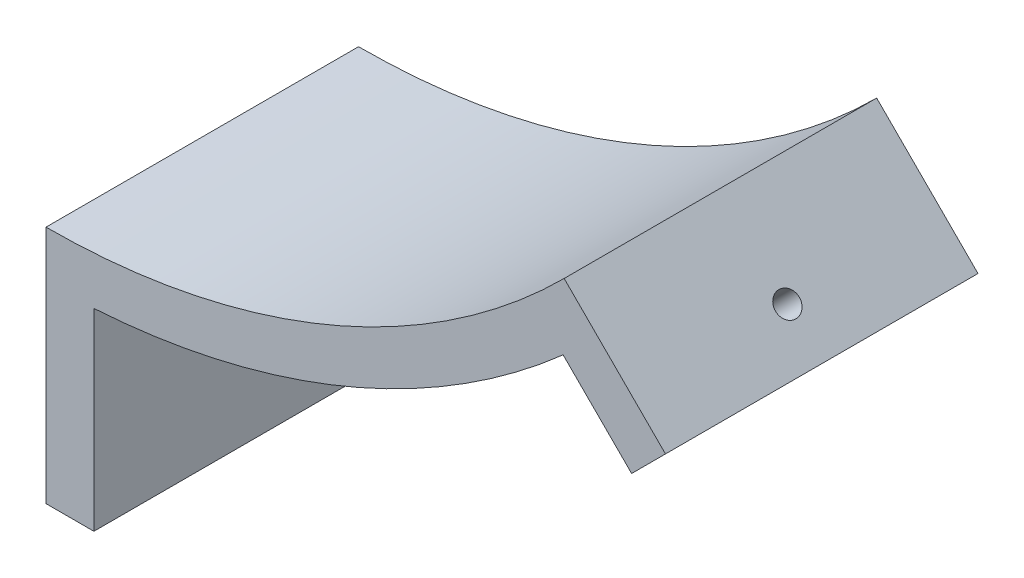
SolidWorks part; units mm, degrees
ref_plane "Alzado" through (0, 0, 0) normal (0, 0, 1) x (1, 0, 0)
ref_plane "Planta" through (0, 0, 0) normal (0, 1, 0) x (1, 0, 0)
ref_plane "Vista lateral" through (0, 0, 0) normal (1, 0, 0) x (0, 0, -1)
sketch "Croquis1" plane through (0, 0, 0) normal (0, 0, 1) x (1, 0, 0)
  line L0 (0, 0) -> (73.1376, 0)
  line L1 (108.1873, -108.1873) -> (129.3428, -129.3428)
  line L4 (0, 0) -> (108.1873, -108.1873)
  line L6 (129.3428, -129.3428) -> (122.2717, -136.4138)
  line L8 (122.2717, -136.4138) -> (107.9702, -122.1124)
  line L15 (0, -153) -> (0, -203)
  line L16 (0, -163) -> (0, -203)
  line L17 (0, -203) -> (10, -203)
  line L18 (10, -203) -> (10, -162.693)
  arc A1 (0, -153) -> (111.6651, -104.594) centre (0, 0) ccw
  arc A2 (10, -162.693) -> (107.9702, -122.1124) centre (0, 0) ccw
  arc A3 (10, -162.693) -> (107.9702, -122.1124) centre (0, 0) ccw
  arc A4 (0, -153) -> (111.6651, -104.594) centre (0, 0) ccw
  dimension "D1" = 45
  dimension "D2" = 10
  dimension "D6" = 326
  dimension "D4" = 50
  dimension "D5" = 10
extrude "Saliente-Extruir1" add sketch "Croquis1" along normal blind 65.25
sketch "Croquis5" plane through (10, 0, 0) normal (1, 0, 0) x (0, 0, -1)
  line L0 (0, -153) -> (0, -203) construction
  line L1 (-65.25, -203) -> (0, -203) construction
  circle A0 centre (-32.625, -183) radius 2.5
  dimension "D1" = 5
  dimension "D2" = 32.625
  dimension "D3" = 20
extrude "Cortar-Extruir3" cut sketch "Croquis5" against normal blind 45
sketch "Croquis6" plane through (0, 0, 0) normal (0.7071, 0.7071, 0) x (0, 0, -1)
  line L0 (-65.25, -153) -> (-65.25, -182.9183) construction
  line L1 (-65.25, -182.9183) -> (0, -182.9183) construction
  circle A0 centre (-32.62, -172.7683) radius 2.5
  dimension "D1" = 32.63
  dimension "D2" = 10.15
extrude "Cortar-Extruir4" cut sketch "Croquis6" against normal blind 12
